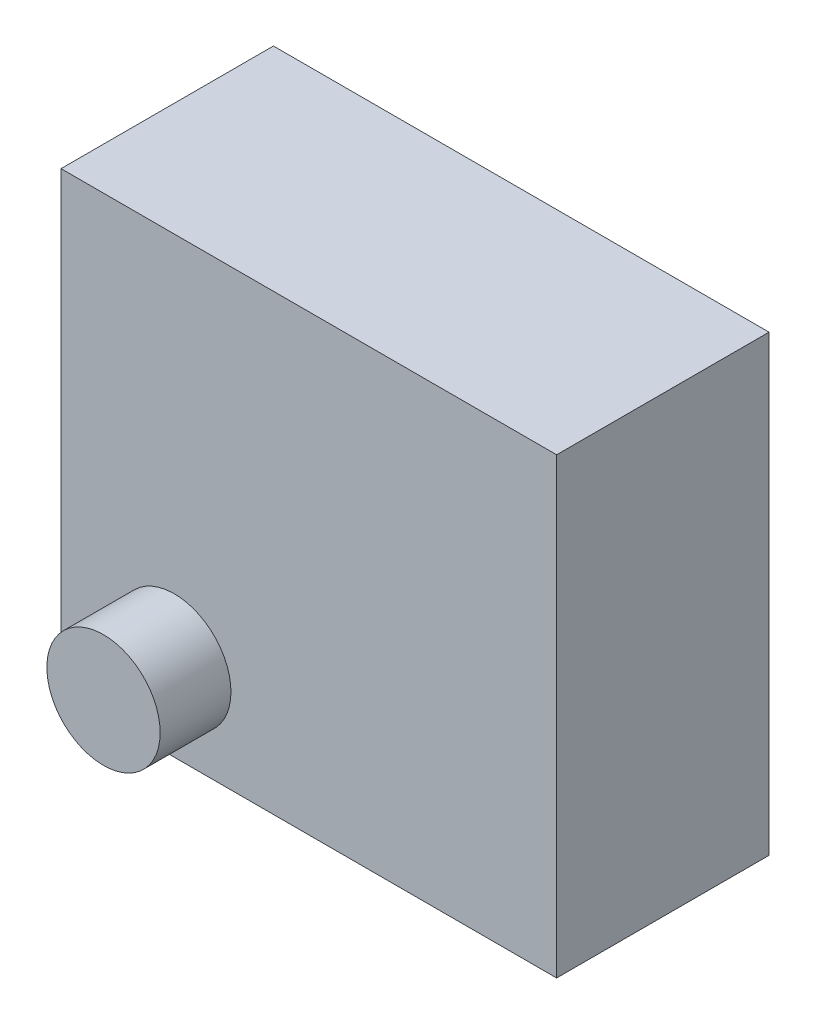
SolidWorks part; units mm, degrees
ref_plane "前视基准面" through (0, 0, 0) normal (0, 0, 1) x (1, 0, 0)
ref_plane "上视基准面" through (0, 0, 0) normal (0, 1, 0) x (1, 0, 0)
ref_plane "右视基准面" through (0, 0, 0) normal (1, 0, 0) x (0, 0, -1)
sketch "草图1" plane through (0, 0, 0) normal (0, 0, 1) x (1, 0, 0)
  line L1 (-175, 160) -> (175, 160)
  line L2 (-175, 160) -> (-175, -160)
  line L3 (-175, -160) -> (175, -160)
  line L4 (175, 160) -> (175, -160)
  line L5 (-175, 160) -> (175, -160) construction
  line L6 (-175, -160) -> (175, 160) construction
  point P0 (0, 0)
  dimension "D1" = 350
  dimension "D2" = 320
extrude "凸台-拉伸1" add sketch "草图1" along normal blind 150
sketch "草图2" plane through (0, 0, 150) normal (0, 0, 1) x (1, 0, 0)
  line L0 (-175, 160) -> (-175, -160) construction
  line L1 (-175, -160) -> (175, -160) construction
  circle A0 centre (-95, -100) radius 40
  dimension "D3" = 80
  dimension "D1" = 80
  dimension "D2" = 60
extrude "凸台-拉伸2" add sketch "草图2" along normal blind 50
